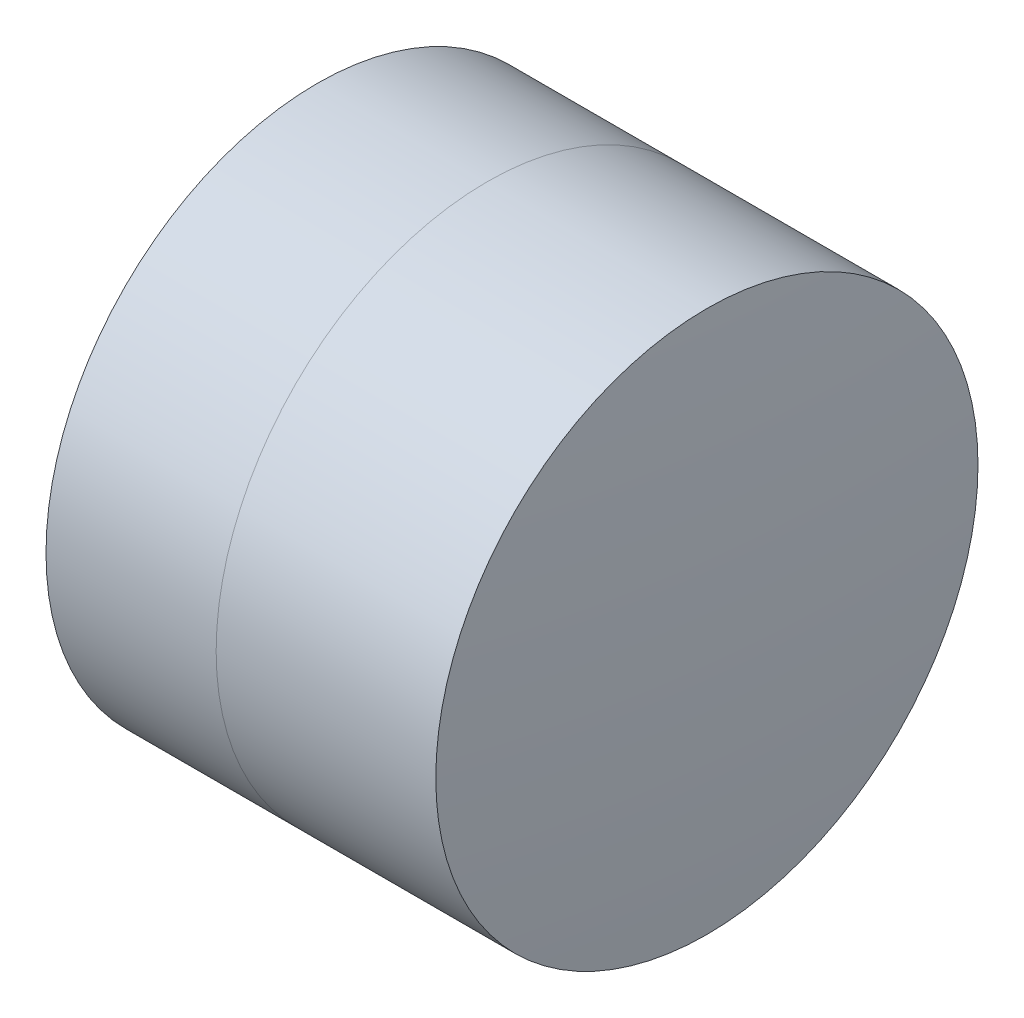
SolidWorks part; units mm, degrees
ref_plane "前视基准面" through (0, 0, 0) normal (0, 0, 1) x (1, 0, 0)
ref_plane "上视基准面" through (0, 0, 0) normal (0, 1, 0) x (1, 0, 0)
ref_plane "右视基准面" through (0, 0, 0) normal (1, 0, 0) x (0, 0, -1)
sketch "草图1" plane through (0, 0, 0) normal (0, 1, 0) x (1, 0, 0)
  line L0 (124.5233, 0) -> (646.9917, 0) construction
  line L1 (261.2402, -2.5) -> (262.8092, -2.5)
  line L2 (261.2402, 2.5) -> (262.8092, 2.5)
  arc A0 (262.8092, -2.5) -> (262.8092, 2.5) centre (255.6321, 0) ccw
  arc A1 (261.2402, 2.5) -> (261.2402, -2.5) centre (271.2321, 0) ccw
  point P10 (260.9321, 0)
  point P11 (263.2321, 0)
  dimension "D3" = 10.3
  dimension "D4" = 7.6
  dimension "D1" = 2.5
  dimension "D2" = 2.5
  dimension "D5" = 2.3
revolve "旋转1" add sketch "草图1" angle 360 about L0
sketch "草图2" plane through (0, 0, 0) normal (0, 1, 0) x (1, 0, 0)
  line L0 (-0.5519, 0) -> (622.6607, 0) construction
  line L2 (262.8092, 2.5) -> (264.8346, 2.5)
  line L3 (262.8092, -2.5) -> (264.8346, -2.5)
  arc A0 (264.8346, -2.5) -> (264.8346, 2.5) centre (232.8321, 0) ccw
  arc A1 (262.8092, -2.5) -> (262.8092, 2.5) centre (255.6321, 0) ccw construction
  arc A2 (262.8092, -2.5) -> (262.8092, 2.5) centre (255.6321, 0) ccw
  point P4 (263.2321, 0)
  point P8 (264.9321, 0)
  dimension "D1" = 32.1
  dimension "D2" = 1.7
revolve "旋转3" add sketch "草图2" angle 360 about L0
